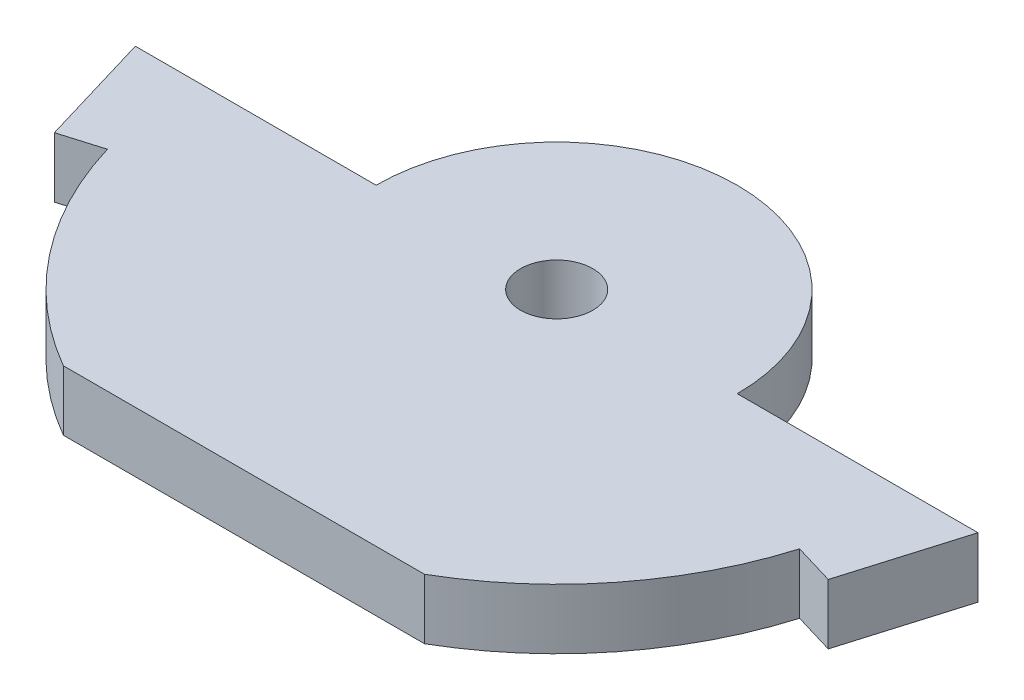
SolidWorks part; units mm, degrees
ref_plane "Front Plane" through (0, 0, 0) normal (0, 0, 1) x (1, 0, 0)
ref_plane "Top Plane" through (0, 0, 0) normal (0, 1, 0) x (1, 0, 0)
ref_plane "Right Plane" through (0, 0, 0) normal (1, 0, 0) x (0, 0, -1)
sketch "Sketch1" plane through (0, 0, 0) normal (0, 1, 0) x (1, 0, 0)
  line L0 (-30, 0) -> (30, 0) construction
  line L1 (-15, 0) -> (-30, 0)
  line L2 (15, 0) -> (30, 0)
  line L3 (-30, 0) -> (-35, 0)
  line L4 (-35, 0) -> (-32.1429, -9.5831)
  line L5 (-32.1429, -9.5831) -> (-28.7494, -8.5714)
  line L6 (-31.305, 0) -> (-28.7494, -8.5714) construction
  line L7 (0, 15) -> (0, 0) construction
  line L8 (31.305, 0) -> (28.7494, -8.5714) construction
  line L9 (32.1429, -9.5831) -> (28.7494, -8.5714)
  line L10 (35, 0) -> (32.1429, -9.5831)
  line L11 (30, 0) -> (35, 0)
  line L12 (-15, -25.9808) -> (15, -25.9808)
  circle A0 centre (0, 0) radius 30 construction
  circle A1 centre (0, 0) radius 3
  arc A2 (-15, 0) -> (15, 0) centre (0, 0) cw
  arc A3 (-28.7494, -8.5714) -> (28.7494, -8.5714) centre (0, 0) ccw
  dimension "D1" = 60
  dimension "D2" = 6
  dimension "D3" = 15
  dimension "D4" = 10
  dimension "D5" = 5
extrude "Boss-Extrude1" add sketch "Sketch1" along normal blind 5 contours L5 A3 L9 L10 L11 L2 A2 L1 L3 L4 A1
